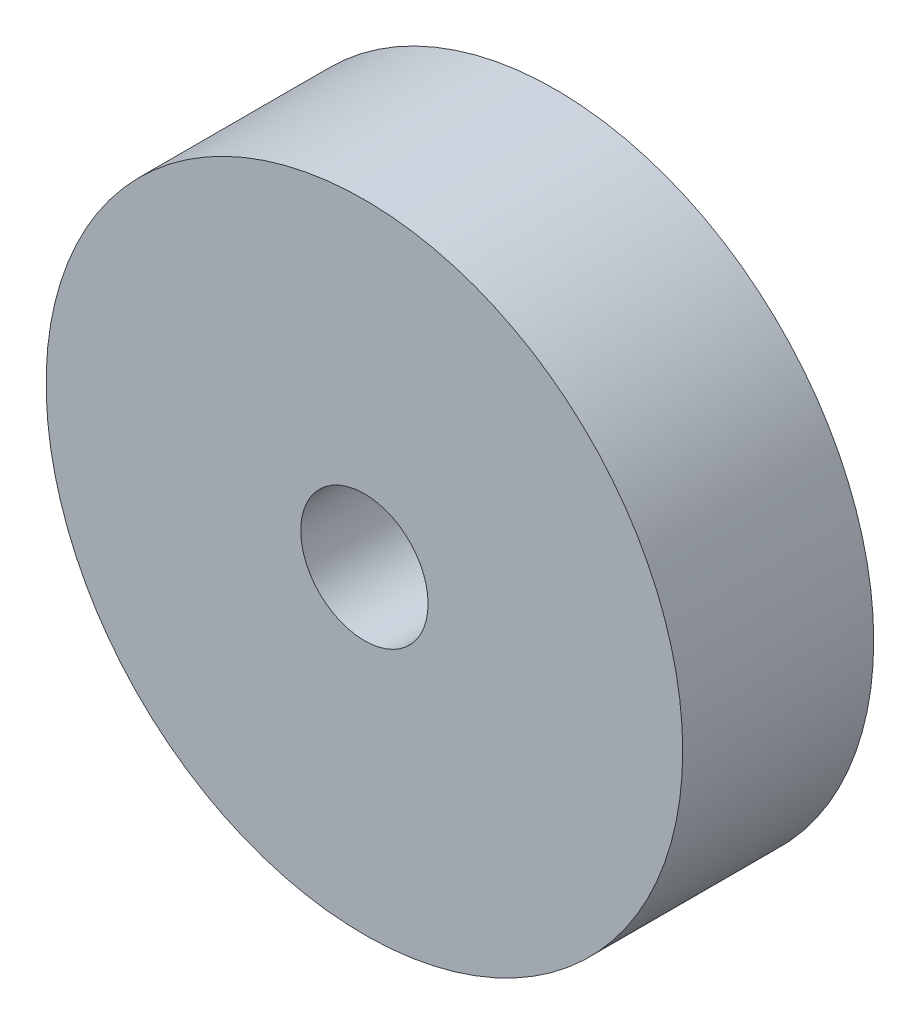
SolidWorks part; units mm, degrees
ref_plane "Front Plane" through (0, 0, 0) normal (0, 0, 1) x (1, 0, 0)
ref_plane "Top Plane" through (0, 0, 0) normal (0, 1, 0) x (1, 0, 0)
ref_plane "Right Plane" through (0, 0, 0) normal (1, 0, 0) x (0, 0, -1)
sketch "Sketch1" plane through (0, 0, 0) normal (0, 0, 1) x (1, 0, 0)
  circle A0 centre (0, 0) radius 20
  dimension "D1" = 40
extrude "Boss-Extrude1" add sketch "Sketch1" along normal blind 12
sketch "Sketch2" plane through (0, 0, 12) normal (0, 0, 1) x (1, 0, 0)
  circle A0 centre (0, 0) radius 4
  circle A1 centre (0, 0) radius 20 construction
  dimension "D1" = 8
extrude "Cut-Extrude1" cut sketch "Sketch2" against normal blind 12
